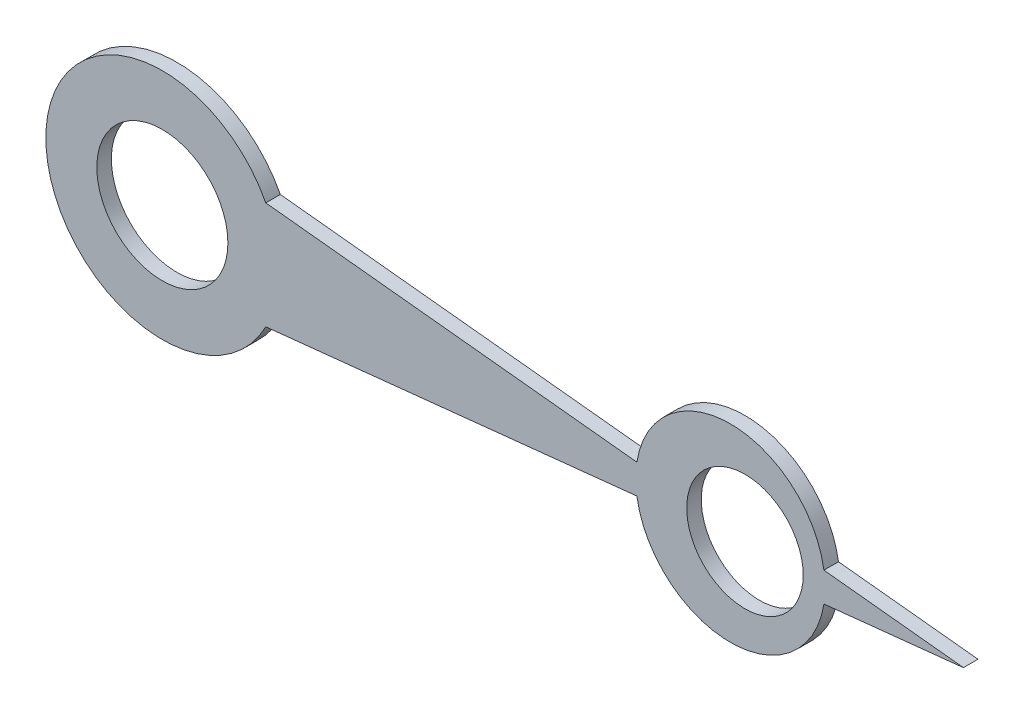
SolidWorks part; units mm, degrees
ref_plane "Front Plane" through (0, 0, 0) normal (0, 0, 1) x (1, 0, 0)
ref_plane "Top Plane" through (0, 0, 0) normal (0, 1, 0) x (1, 0, 0)
ref_plane "Right Plane" through (0, 0, 0) normal (1, 0, 0) x (0, 0, -1)
sketch "Sketch2" plane through (0, 0, 0) normal (0, 0, 1) x (1, 0, 0)
  line L0 (0, 0) -> (55, 0) construction
  line L1 (0, 0) -> (55, 0) construction
  line L2 (55, 0) -> (45.4216, -1.0067)
  line L3 (7.101, -3.6845) -> (32.5784, -1.0067)
  line L4 (55, 0) -> (45.4216, 1.0067)
  line L5 (7.101, 3.6845) -> (32.5784, 1.0067)
  circle A0 centre (0, 0) radius 4.5 construction
  circle A1 centre (0, 0) radius 4.5
  circle A2 centre (40, 0) radius 4
  arc A3 (32.5784, -1.0067) -> (45.4216, -1.0067) centre (39, 0) ccw
  arc A4 (7.101, 3.6845) -> (7.101, -3.6845) centre (0, 0) ccw
  arc A5 (45.4216, 1.0067) -> (32.5784, 1.0067) centre (39, 0) ccw
  dimension "D1" = 8
  dimension "D2" = 13
  dimension "D6" = 16
  dimension "D3" = 1
  dimension "D4" = 15
  dimension "D5" = 6
  dimension "D7" = 6
extrude "Boss-Extrude1" add sketch "Sketch2" along normal up to vertex (20 mm away) from vertex at 19
equation "\"D7@Sketch2\"=\"D5@Sketch2\""
